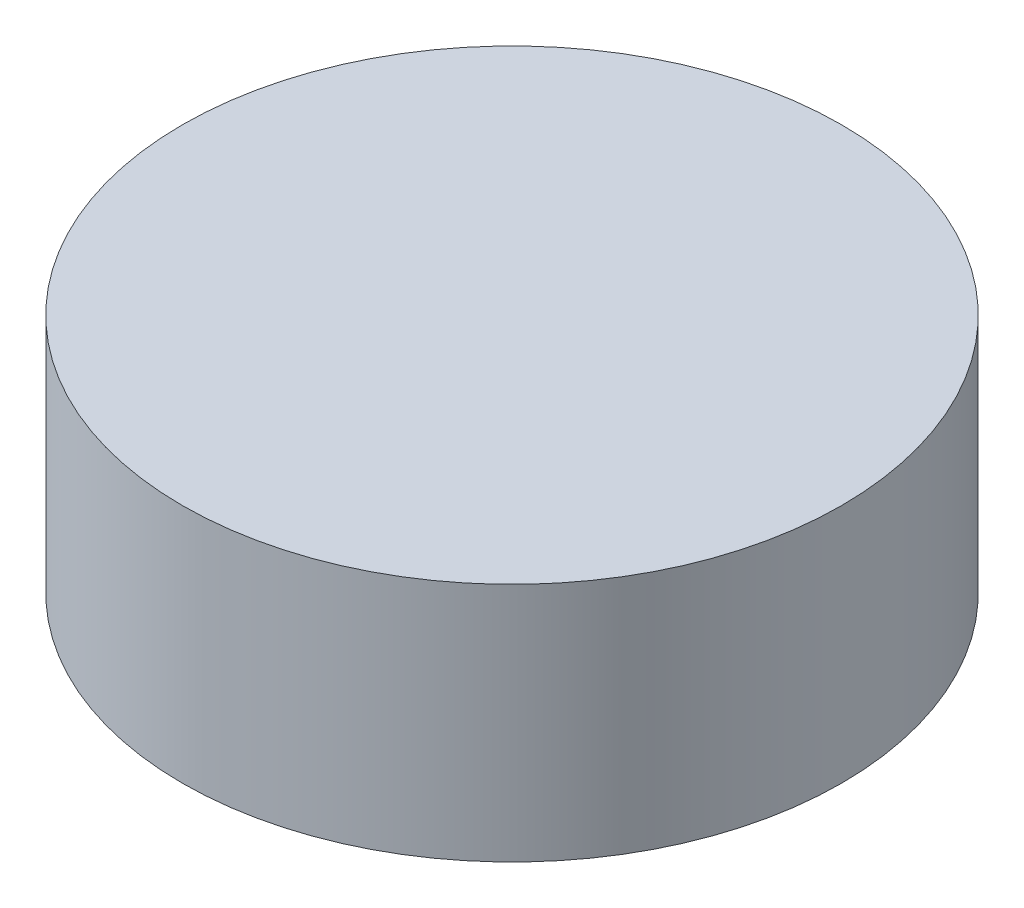
SolidWorks part; units mm, degrees
ref_plane "Front Plane" through (0, 0, 0) normal (0, 0, 1) x (1, 0, 0)
ref_plane "Top Plane" through (0, 0, 0) normal (0, 1, 0) x (1, 0, 0)
ref_plane "Right Plane" through (0, 0, 0) normal (1, 0, 0) x (0, 0, -1)
sketch "Sketch1" plane through (0, 0, 0) normal (0, 1, 0) x (1, 0, 0)
  circle A0 centre (0, 0) radius 127.5
  dimension "D1" = 255
extrude "Extrude1" add sketch "Sketch1" along normal blind 93
